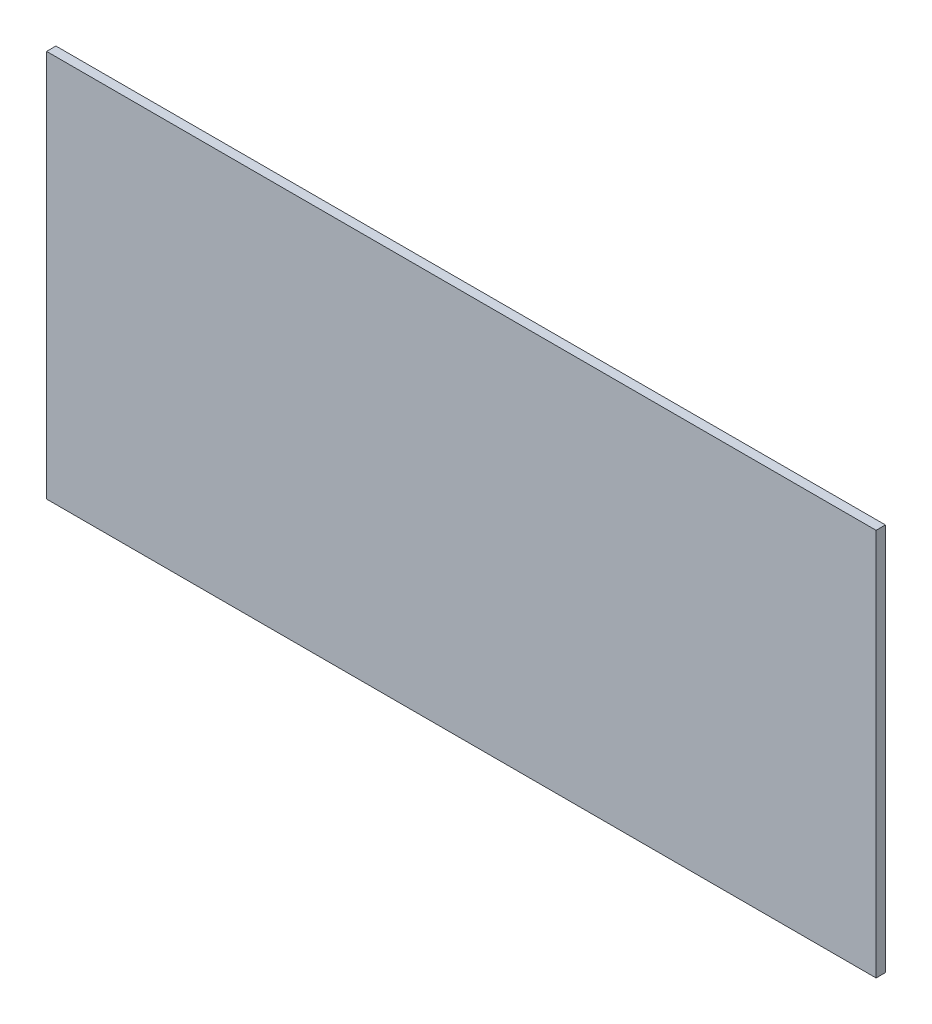
SolidWorks part; units mm, degrees
material "ABS PC"
ref_plane "Front Plane" through (0, 0, 0) normal (0, 0, 1) x (1, 0, 0)
ref_plane "Top Plane" through (0, 0, 0) normal (0, 1, 0) x (1, 0, 0)
ref_plane "Right Plane" through (0, 0, 0) normal (1, 0, 0) x (0, 0, -1)
sketch "Sketch1" plane through (0, 0, 0) normal (0, 0, 1) x (1, 0, 0)
  line L5 (30.5422, 186.9471) -> (30.5422, 181.6639)
  line L8 (41.8452, 186.9471) -> (30.5422, 186.9471)
  line L10 (30.5422, 181.6639) -> (41.8452, 181.6639)
  line L11 (41.8452, 181.6639) -> (41.8452, 186.9471)
  dimension "D1" = 5.2832
  dimension "D2" = 11.303
extrude "Boss-Extrude1" add sketch "Sketch1" along normal blind 0.127
